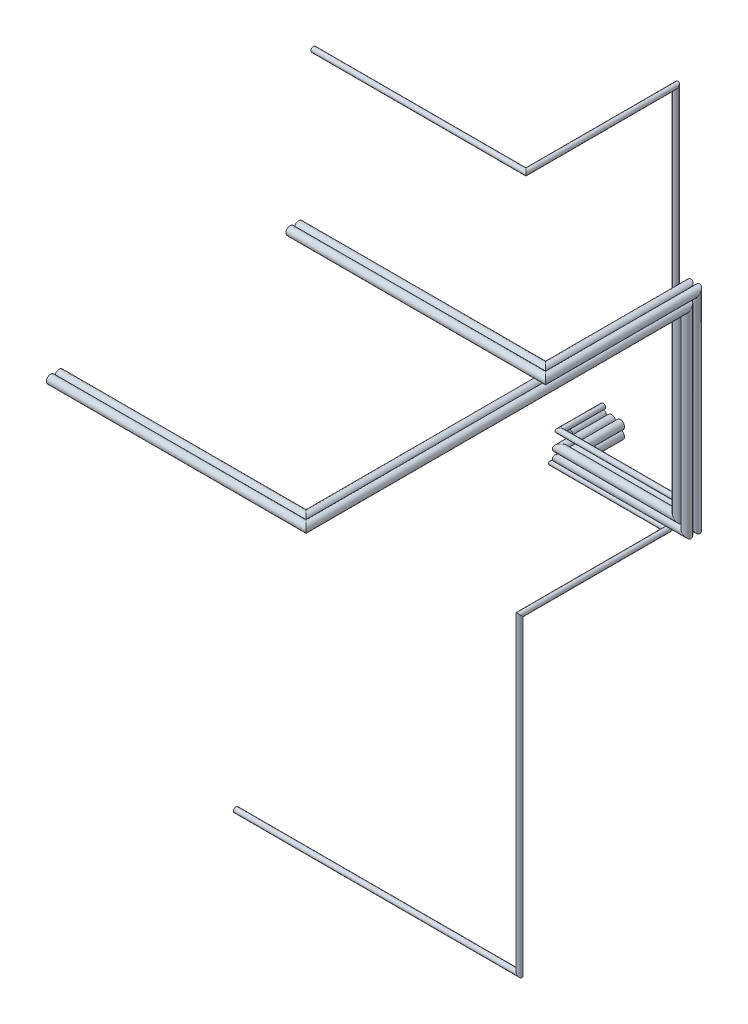
SolidWorks part; units mm, degrees
ref_plane "Front Plane" through (0, 0, 0) normal (0, 0, 1) x (1, 0, 0)
ref_plane "Top Plane" through (0, 0, 0) normal (0, 1, 0) x (1, 0, 0)
ref_plane "Right Plane" through (0, 0, 0) normal (1, 0, 0) x (0, 0, -1)
sketch "Sketch1" plane through (0, 0, 0) normal (0, 0, 1) x (1, 0, 0)
  circle A0 centre (0, 0) radius 50
  circle A1 centre (104.6203, 0) radius 50
  circle A3 centre (104.6203, 101.6323) radius 50
  circle A5 centre (0, 101.6323) radius 50
  circle A6 centre (209.2405, 0) radius 50 [skipped]
  circle A7 centre (209.2405, 101.6323) radius 50 [skipped]
  dimension "D1" = 3
  dimension "D2" = 2
sketch3d "3DSketch1"
  line L0 (0, 0, 0) -> (0, 0, 600)
  line L1 (0, 0, 600) -> (1490, 0, 600)
  line L2 (1490, 0, 600) -> (1490, 2300, 600)
  line L3 (1490, 2300, 600) -> (1490, 2300, 2000)
  dimension "D1" = 600
  dimension "D2" = 1400
  dimension "D3" = 2300
  dimension "D4" = 1490
sweep "Sweep1" add profiles "Sketch1" path "3DSketch1"
sketch "Sketch2" plane through (0, 0, 800) normal (0, 0, 1) x (1, 0, 0)
  circle A1 centre (1490, 2404.6203) radius 50
  circle A2 centre (1388.3677, 2404.6203) radius 50
sketch3d "3DSketch2"
  line L0 (1220.6865, 2359.359, 800) -> (1220.6865, 2359.359, 2000)
  line L1 (1220.6865, 2359.359, 2000) -> (-1529.3135, 2359.359, 2000)
  dimension "D1" = 1200
  dimension "D2" = 2750
sweep "Sweep3" add profiles "Sketch2" path "3DSketch2"
sketch "Sketch3" plane through (0, 0, 800) normal (0, 0, 1) x (1, 0, 0)
  circle A0 centre (1490, 2300) radius 50
  circle A2 centre (1388.3677, 2300) radius 50
sketch3d "3DSketch3"
  line L0 (1490, 2300, 800) -> (1490, 2300, 5100)
  line L1 (1490, 2300, 5100) -> (-1529.3135, 2300, 5100)
  circle A1 centre (1490, 2300, 800) radius 50 construction
  point P5 (1490, 2300, 850)
sweep "Sweep4" add profiles "Sketch3" path "3DSketch3"
sketch "Sketch4" plane through (0, 0, 0) normal (0, 0, -1) x (-1, 0, 0)
  circle A0 centre (104.9294, 0) radius 50
  circle A1 centre (104.9294, 105) radius 50
  dimension "D1" = 100
  dimension "D2" = 100
  dimension "D3" = 105
extrude "Boss-Extrude1" add sketch "Sketch4" against normal blind 400 separate body
sketch "Sketch5" plane through (0, 0, 0) normal (0, 0, -1) x (-1, 0, 0)
  circle A0 centre (99.2922, 188.1121) radius 30
  circle A1 centre (99.2922, -103.9964) radius 30
  dimension "D1" = 60
  dimension "D2" = 60
extrude "Boss-Extrude2" add sketch "Sketch5" against normal blind 400 separate body
sketch3d "3DSketch4"
  line L0 (-100.4299, 158.1337, 400) -> (-100.4299, 158.1337, 510.9908)
  line L3 (-100.4299, 158.1337, 510.9908) -> (1299.5701, 158.1337, 510.9908)
  line L4 (1299.5701, 158.1337, 510.9908) -> (1299.5701, 4408.1337, 510.9908)
  line L5 (1299.5701, 4408.1337, 510.9908) -> (1299.5701, 4408.1337, 2310.9908)
  line L6 (1299.5701, 4408.1337, 2310.9908) -> (-1241.5638, 4408.1337, 2310.9908)
  circle A0 centre (-99.2922, 188.1121, 400) radius 30 construction
  point P4 (-99.2922, 188.1121, 370)
  dimension "D1" = 4250
  dimension "D2" = 1800
  dimension "D3" = 1400
sketch "Sketch6" plane through (0, 0, 400) normal (0, 0, 1) x (1, 0, 0)
  circle A0 centre (-99.2922, 188.1121) radius 30
sweep "Sweep5" add profiles "Sketch6" path "3DSketch4"
sketch "Sketch7" plane through (0, 0, 400) normal (0, 0, 1) x (1, 0, 0)
  circle A0 centre (-99.2922, -103.9964) radius 30
sketch3d "3DSketch5"
  line L0 (-99.2922, -103.9964, 400) -> (-99.2922, -103.9964, 587.6533)
  line L1 (-99.2922, -103.9964, 587.6533) -> (1250.7078, -103.9964, 587.6533)
  line L2 (1250.7078, -103.9964, 587.6533) -> (1250.7078, -103.9964, 2337.6533)
  line L3 (1250.7078, -3775.4046, 2337.6533) -> (-2100.968, -3775.4046, 2337.6533)
  line L4 (1250.7078, -103.9964, 2337.6533) -> (1250.7078, -3775.4046, 2337.6533)
  dimension "D1" = 1750
  dimension "D2" = 1350
sweep "Sweep6" add profiles "Sketch7" path "3DSketch5"
